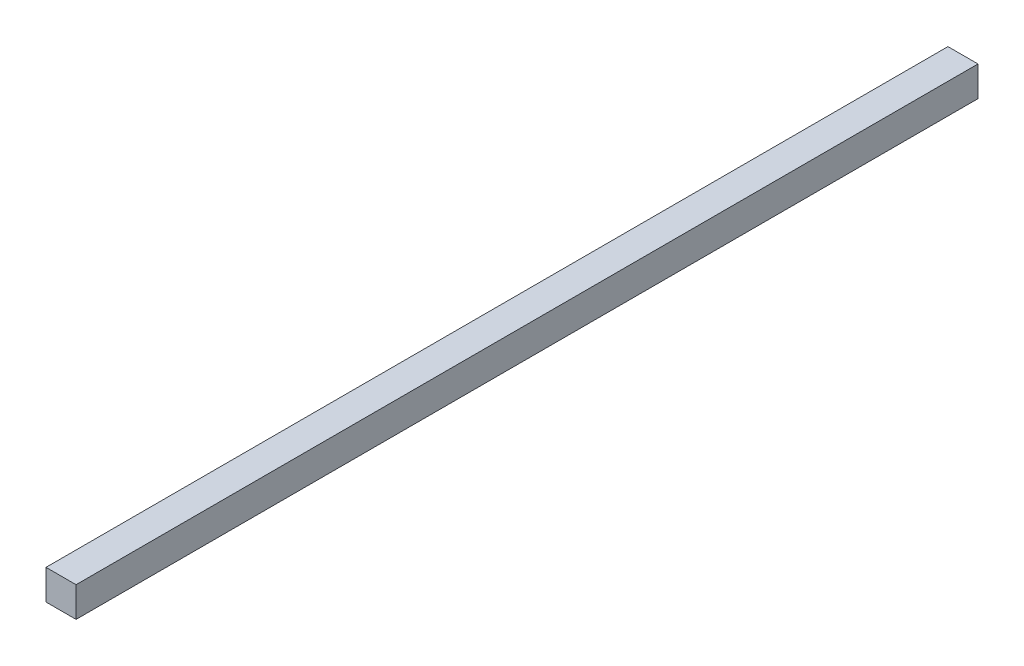
SolidWorks part; units mm, degrees
ref_plane "Plan de face" through (0, 0, 0) normal (0, 0, 1) x (1, 0, 0)
ref_plane "Plan de dessus" through (0, 0, 0) normal (0, 1, 0) x (1, 0, 0)
ref_plane "Plan de droite" through (0, 0, 0) normal (1, 0, 0) x (0, 0, -1)
sketch "Esquisse1" plane through (0, 0, 0) normal (0, 0, 1) x (1, 0, 0)
  line L1 (-17.9387, 5) -> (-7.9387, 5)
  line L2 (-17.9387, 5) -> (-17.9387, -5)
  line L3 (-17.9387, -5) -> (-7.9387, -5)
  line L4 (-7.9387, 5) -> (-7.9387, -5)
  dimension "D1" = 10
  dimension "D2" = 10
extrude "Boss.-Extru.1" add sketch "Esquisse1" along normal blind 300
